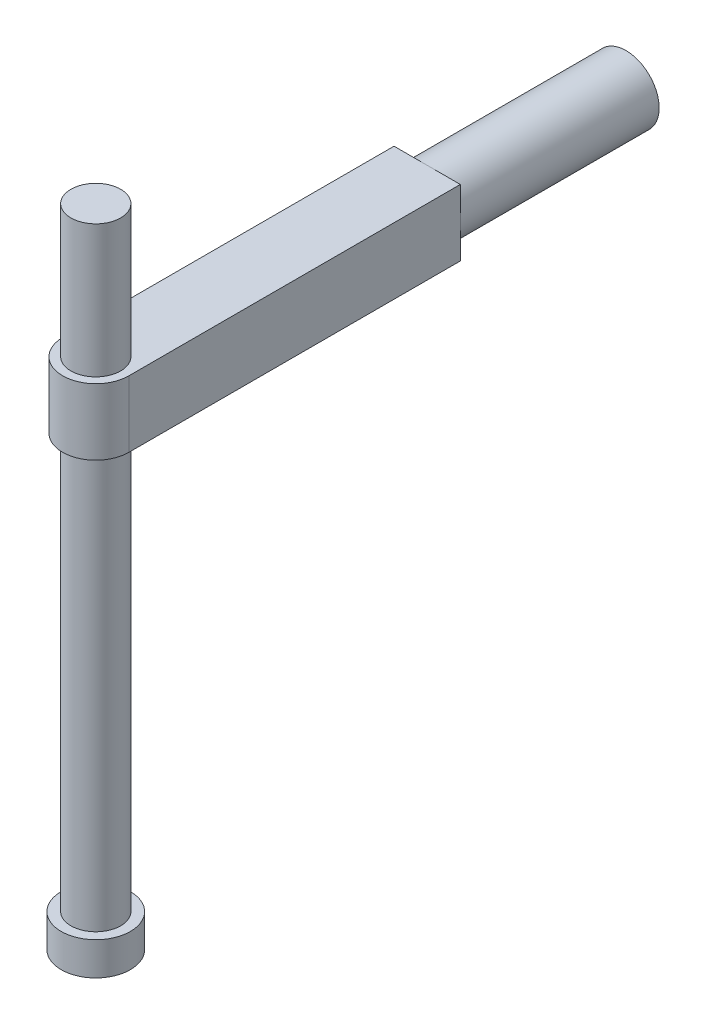
SolidWorks part; units mm, degrees
ref_plane "Front Plane" through (0, 0, 0) normal (0, 0, 1) x (1, 0, 0)
ref_plane "Top Plane" through (0, 0, 0) normal (0, 1, 0) x (1, 0, 0)
ref_plane "Right Plane" through (0, 0, 0) normal (1, 0, 0) x (0, 0, -1)
sketch "Sketch1" plane through (0, 0, 0) normal (0, 1, 0) x (1, 0, 0)
  line L0 (0, 0) -> (0, 20) construction
  line L1 (-2, 0) -> (-2, 20)
  line L2 (2, 0) -> (2, 20)
  arc A0 (-2, 0) -> (2, 0) centre (0, 0) ccw
  arc A1 (2, 20) -> (-2, 20) centre (0, 20) ccw
  point P3 (0, 10)
  dimension "D2" = 2
  dimension "D1" = 20
extrude "Boss-Extrude1" add sketch "Sketch1" along normal blind 4
ref_plane "Plane1" through (0, 12, 0) normal (0, 1, 0) x (1, 0, 0)
sketch "Sketch2" plane through (0, 12, 0) normal (0, 1, 0) x (1, 0, 0)
  circle A0 centre (0, 0) radius 1.5
  dimension "D1" = 3
extrude "Boss-Extrude2" add sketch "Sketch2" against normal blind 37
sketch "Sketch3" plane through (0, -25, 0) normal (0, -1, 0) x (1, 0, 0)
  circle A0 centre (0, 0) radius 2.0861
extrude "Boss-Extrude3" add sketch "Sketch3" along normal blind 2
sketch "Sketch4" plane through (0, 4, 0) normal (0, 1, 0) x (1, 0, 0)
  line L1 (-2, 20) -> (3, 20)
  line L2 (-2, 20) -> (-2, 23.5763)
  line L3 (-2, 23.5763) -> (3, 23.5763)
  line L4 (3, 20) -> (3, 23.5763)
extrude "Cut-Extrude1" cut sketch "Sketch4" against normal through all
sketch "Sketch5" plane through (0, 0, -20) normal (0, 0, -1) x (-1, 0, 0)
  line L0 (2, 4) -> (2, 0) construction
  line L1 (2, 4) -> (-2, 4) construction
  circle A0 centre (0, 2) radius 2
  dimension "D1" = 4
  dimension "D2" = 2
extrude "Boss-Extrude4" add sketch "Sketch5" along normal blind 12
ref_plane "Plane2" through (0, 0, -30) normal (0, 0, -1) x (-1, 0, 0)
sketch "Sketch7" plane through (0, 0, -30) normal (0, 0, -1) x (-1, 0, 0)
  point P0 (0, 2)
